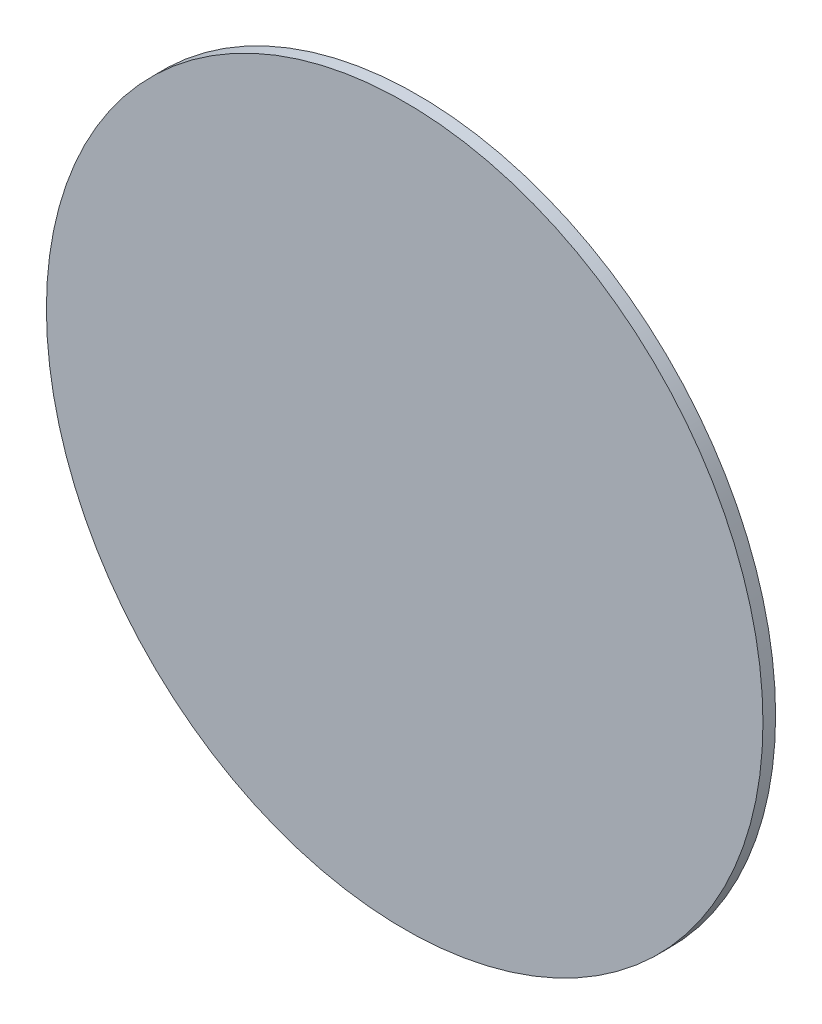
SolidWorks part; units mm, degrees
ref_plane "Front" through (0, 0, 0) normal (0, 0, 1) x (1, 0, 0)
ref_plane "Top" through (0, 0, 0) normal (0, 1, 0) x (1, 0, 0)
ref_plane "Right" through (0, 0, 0) normal (1, 0, 0) x (0, 0, -1)
sketch "Sketch1" plane through (0, 0, 0) normal (0, 0, 1) x (1, 0, 0)
  circle A0 centre (0, 0) radius 85
  dimension "D1" = 170
extrude "Boss-Extrude1" add sketch "Sketch1" along normal blind 3
